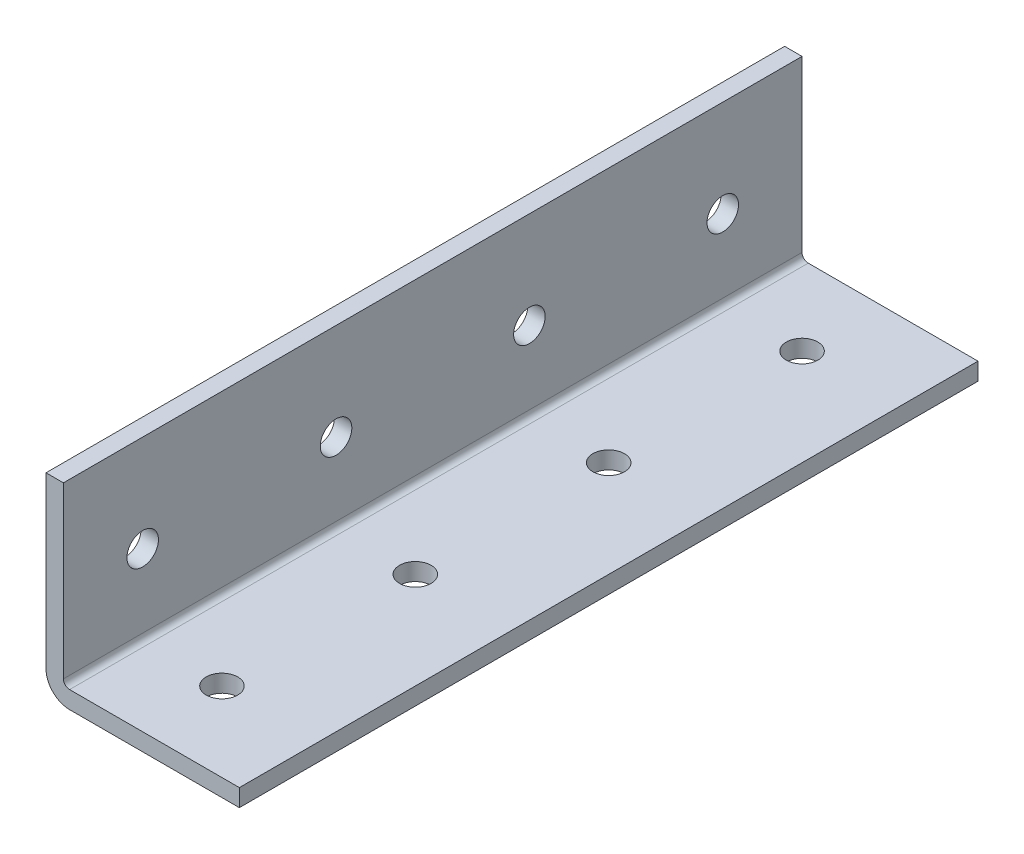
SolidWorks part; units mm, degrees
material "6061-T6 (SS)"
ref_plane "Front Plane" through (0, 0, 0) normal (0, 0, 1) x (1, 0, 0)
ref_plane "Top Plane" through (0, 0, 0) normal (0, 1, 0) x (1, 0, 0)
ref_plane "Right Plane" through (0, 0, 0) normal (1, 0, 0) x (0, 0, -1)
ref_plane "Plane1" through (0, 0, 0) normal (-1, 0, 0) x (0, -1, 0)
sketch "Sketch1" plane through (0, 0, 0) normal (-1, 0, 0) x (0, -1, 0)
  line L0 (0, 749.3) -> (-25.4, 749.3)
  line L1 (-25.4, 749.3) -> (-25.4, -749.3)
  line L2 (-25.4, -749.3) -> (0, -749.3)
  line L3 (0, -749.3) -> (0, 749.3)
extrude "Boss-Extrude1" add sketch "Sketch1" against normal blind 25.4
sketch "Sketch2" plane through (0, 0, -749.3) normal (0, 0, -1) x (-1, 0, 0)
  line L0 (-25.4, 2.286) -> (-2.286, 2.286)
  line L1 (-2.286, 2.286) -> (-2.286, 25.4)
  line L2 (-2.286, 25.4) -> (-25.4, 25.4)
  line L3 (-25.4, 25.4) -> (-25.4, 2.286)
extrude "Cut-Extrude1" cut sketch "Sketch2" against normal through all
hole_wizard "M3.5 Clearance Hole1" positions "Sketch4" profile "Sketch3" hole size "M3.5" standard "ANSI Metric"
sketch "Sketch4" plane through (0, 0, 0) normal (0, -1, 0) x (-1, 0, 0)
  point P0 (-12.7, 736.6)
  point P1 (-12.7, 711.2)
  point P2 (-12.7, 685.8)
  point P3 (-12.7, 660.4)
  point P4 (-12.7, 635)
  point P5 (-12.7, 609.6)
  point P6 (-12.7, 584.2)
  point P7 (-12.7, 558.8)
  point P8 (-12.7, 533.4)
  point P9 (-12.7, 508)
  point P10 (-12.7, 482.6)
  point P11 (-12.7, 457.2)
  point P12 (-12.7, 431.8)
  point P13 (-12.7, 406.4)
  point P14 (-12.7, 381)
  point P15 (-12.7, 355.6)
  point P16 (-12.7, 330.2)
  point P17 (-12.7, 304.8)
  point P18 (-12.7, 279.4)
  point P19 (-12.7, 254)
  point P20 (-12.7, 228.6)
  point P21 (-12.7, 203.2)
  point P22 (-12.7, 177.8)
  point P23 (-12.7, 152.4)
  point P24 (-12.7, 127)
  point P25 (-12.7, 101.6)
  point P26 (-12.7, 76.2)
  point P27 (-12.7, 50.8)
  point P28 (-12.7, 25.4)
  point P29 (-12.7, 0)
  point P30 (-12.7, -25.4)
  point P31 (-12.7, -50.8)
  point P32 (-12.7, -76.2)
  point P33 (-12.7, -101.6)
  point P34 (-12.7, -127)
  point P35 (-12.7, -152.4)
  point P36 (-12.7, -177.8)
  point P37 (-12.7, -203.2)
  point P38 (-12.7, -228.6)
  point P39 (-12.7, -254)
  point P40 (-12.7, -279.4)
  point P41 (-12.7, -304.8)
  point P42 (-12.7, -330.2)
  point P43 (-12.7, -355.6)
  point P44 (-12.7, -381)
  point P45 (-12.7, -406.4)
  point P46 (-12.7, -431.8)
  point P47 (-12.7, -457.2)
  point P48 (-12.7, -482.6)
  point P49 (-12.7, -508)
  point P50 (-12.7, -533.4)
  point P51 (-12.7, -558.8)
  point P52 (-12.7, -584.2)
  point P53 (-12.7, -609.6)
  point P54 (-12.7, -635)
  point P55 (-12.7, -660.4)
  point P56 (-12.7, -685.8)
  point P57 (-12.7, -711.2)
  point P58 (-12.7, -736.6)
sketch "Sketch3" plane through (12.7, 0, -736.6) normal (1, 0, 0) x (0, 0, -1)
  line L0 (0, 0) -> (0, 25.4)
  line L1 (0, 25.4) -> (2.0701, 25.4)
  line L2 (2.0701, 25.4) -> (2.0701, 0)
  line L5 (2.0701, 0) -> (0, 0)
  line L11 (0, -6.35) -> (0, 107.95) construction
  dimension "Thru Hole Dia." = 4.1402
  dimension "Thru Hole Depth" = 25.4
hole_wizard "M3.5 Clearance Hole2" positions "Sketch6" profile "Sketch5" hole size "M3.5" standard "ANSI Metric"
sketch "Sketch6" plane through (0, 0, 0) normal (-1, 0, 0) x (0, 0, 1)
  point P0 (711.2, 12.7)
  point P1 (736.6, 12.7)
  point P2 (685.8, 12.7)
  point P3 (660.4, 12.7)
  point P4 (635, 12.7)
  point P5 (609.6, 12.7)
  point P6 (584.2, 12.7)
  point P7 (558.8, 12.7)
  point P8 (533.4, 12.7)
  point P9 (508, 12.7)
  point P10 (482.6, 12.7)
  point P11 (457.2, 12.7)
  point P12 (431.8, 12.7)
  point P13 (406.4, 12.7)
  point P14 (381, 12.7)
  point P15 (355.6, 12.7)
  point P16 (330.2, 12.7)
  point P17 (304.8, 12.7)
  point P18 (279.4, 12.7)
  point P19 (254, 12.7)
  point P20 (228.6, 12.7)
  point P21 (203.2, 12.7)
  point P22 (177.8, 12.7)
  point P23 (152.4, 12.7)
  point P24 (127, 12.7)
  point P25 (101.6, 12.7)
  point P26 (76.2, 12.7)
  point P27 (50.8, 12.7)
  point P28 (25.4, 12.7)
  point P29 (0, 12.7)
  point P30 (-25.4, 12.7)
  point P31 (-50.8, 12.7)
  point P32 (-76.2, 12.7)
  point P33 (-101.6, 12.7)
  point P34 (-127, 12.7)
  point P35 (-152.4, 12.7)
  point P36 (-177.8, 12.7)
  point P37 (-203.2, 12.7)
  point P38 (-228.6, 12.7)
  point P39 (-254, 12.7)
  point P40 (-279.4, 12.7)
  point P41 (-304.8, 12.7)
  point P42 (-330.2, 12.7)
  point P43 (-355.6, 12.7)
  point P44 (-381, 12.7)
  point P45 (-406.4, 12.7)
  point P46 (-431.8, 12.7)
  point P47 (-457.2, 12.7)
  point P48 (-482.6, 12.7)
  point P49 (-508, 12.7)
  point P50 (-533.4, 12.7)
  point P51 (-558.8, 12.7)
  point P52 (-584.2, 12.7)
  point P53 (-609.6, 12.7)
  point P54 (-635, 12.7)
  point P55 (-660.4, 12.7)
  point P56 (-685.8, 12.7)
  point P57 (-711.2, 12.7)
  point P58 (-736.6, 12.7)
sketch "Sketch5" plane through (0, 12.7, 711.2) normal (0, 1, 0) x (0, 0, 1)
  line L0 (0, 0) -> (0, 25.4)
  line L1 (0, 25.4) -> (2.0701, 25.4)
  line L2 (2.0701, 25.4) -> (2.0701, 0)
  line L5 (2.0701, 0) -> (0, 0)
  line L11 (0, -6.35) -> (0, 107.95) construction
  dimension "Thru Hole Dia." = 4.1402
  dimension "Thru Hole Depth" = 25.4
chamfer "Chamfer1" distance 2.159 angle 45 4 edges at (25.4, 1.143, -749.3) (1.143, 25.4, -749.3) (1.143, 25.4, 749.3) (25.4, 1.143, 749.3)
fillet "Fillet1" radius 0.8128 1 edges at (2.286, 2.286, 0)
fillet "Fillet2" radius 3.0988 1 edges at (0, 0, 0)
sketch "Sketch8" plane through (0, 0, 749.3) normal (0, 0, 1) x (1, 0, 0)
  line L1 (-45.6555, -36.5704) -> (50.2275, -36.5704)
  line L2 (-45.6555, -36.5704) -> (-45.6555, 42.768)
  line L3 (-45.6555, 42.768) -> (50.2275, 42.768)
  line L4 (50.2275, -36.5704) -> (50.2275, 42.768)
  line L5 (-45.6555, -36.5704) -> (50.2275, 42.768) construction
  line L6 (-45.6555, 42.768) -> (50.2275, -36.5704) construction
  point P0 (2.286, 3.0988)
extrude "Cut-Extrude3" cut sketch "Sketch8" against normal blind 1397
sketch "Sketch9" plane through (0, 0, -647.7) normal (0, 0, 1) x (1, 0, 0)
  line L1 (-26.256, -28.3041) -> (29.3919, -28.3041)
  line L2 (-26.256, -28.3041) -> (-26.256, 31.3553)
  line L3 (-26.256, 31.3553) -> (29.3919, 31.3553)
  line L4 (29.3919, -28.3041) -> (29.3919, 31.3553)
  line L5 (-26.256, -28.3041) -> (29.3919, 31.3553) construction
  line L6 (-26.256, 31.3553) -> (29.3919, -28.3041) construction
  point P0 (1.568, 1.5256)
extrude "Cut-Extrude4" cut sketch "Sketch9" against normal blind 2.286
sketch "Sketch10" plane through (0, 0, -749.3) normal (0, 0, -1) x (-1, 0, 0)
  line L1 (29.0935, -23.4633) -> (-31.0868, -23.4633)
  line L2 (29.0935, -23.4633) -> (29.0935, 30.0694)
  line L3 (29.0935, 30.0694) -> (-31.0868, 30.0694)
  line L4 (-31.0868, -23.4633) -> (-31.0868, 30.0694)
  line L5 (29.0935, -23.4633) -> (-31.0868, 30.0694) construction
  line L6 (29.0935, 30.0694) -> (-31.0868, -23.4633) construction
  point P0 (-0.9966, 3.3031)
extrude "Cut-Extrude5" cut sketch "Sketch10" against normal blind 2.286
